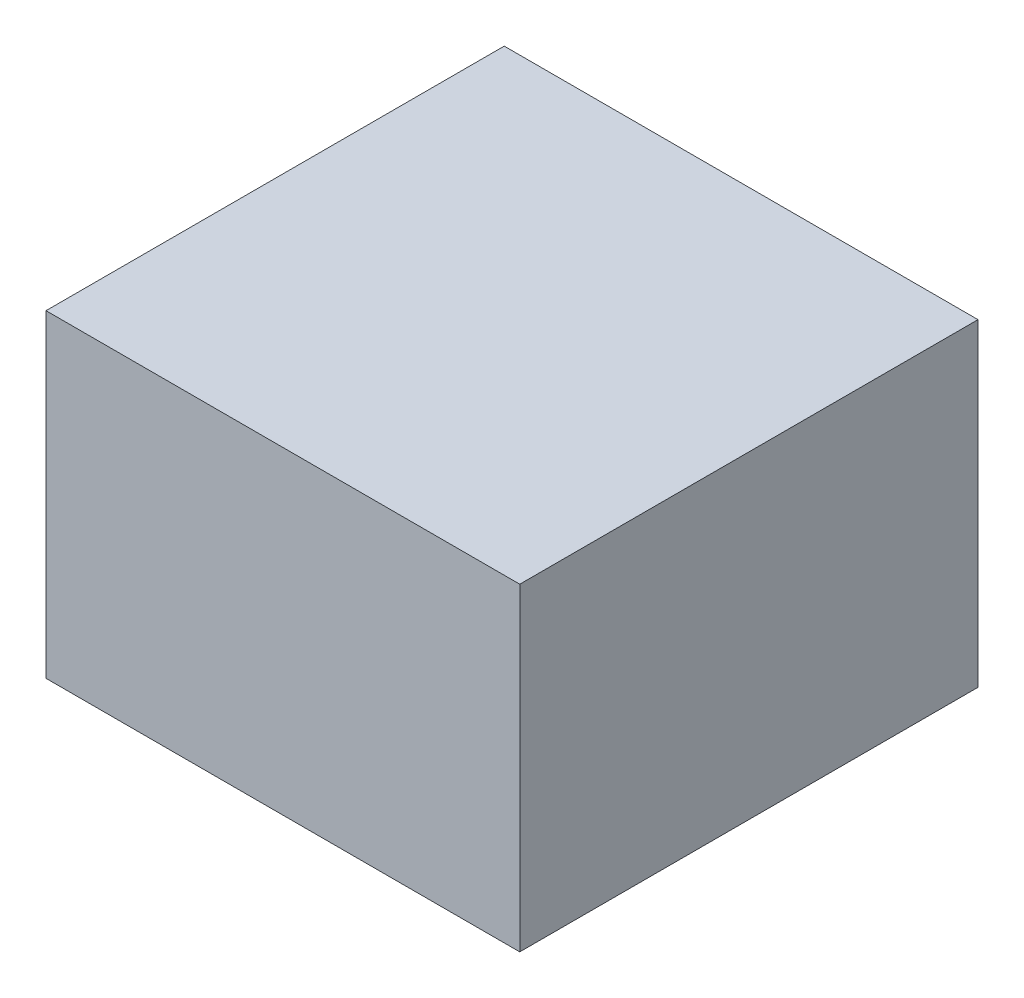
SolidWorks part; units mm, degrees
ref_plane "Front Plane" through (0, 0, 0) normal (0, 0, 1) x (1, 0, 0)
ref_plane "Top Plane" through (0, 0, 0) normal (0, 1, 0) x (1, 0, 0)
ref_plane "Right Plane" through (0, 0, 0) normal (1, 0, 0) x (0, 0, -1)
sketch "Sketch1" plane through (0, 0, 0) normal (0, 0, 1) x (1, 0, 0)
  line L1 (-7.747, -5.207) -> (7.747, -5.207)
  line L2 (-7.747, -5.207) -> (-7.747, 5.207)
  line L3 (-7.747, 5.207) -> (7.747, 5.207)
  line L4 (7.747, -5.207) -> (7.747, 5.207)
  line L5 (-7.747, -5.207) -> (7.747, 5.207) construction
  line L6 (-7.747, 5.207) -> (7.747, -5.207) construction
  point P0 (0, 0)
  dimension "D1" = 15.494
  dimension "D2" = 10.414
extrude "Boss-Extrude1" add sketch "Sketch1" along normal blind 14.986
